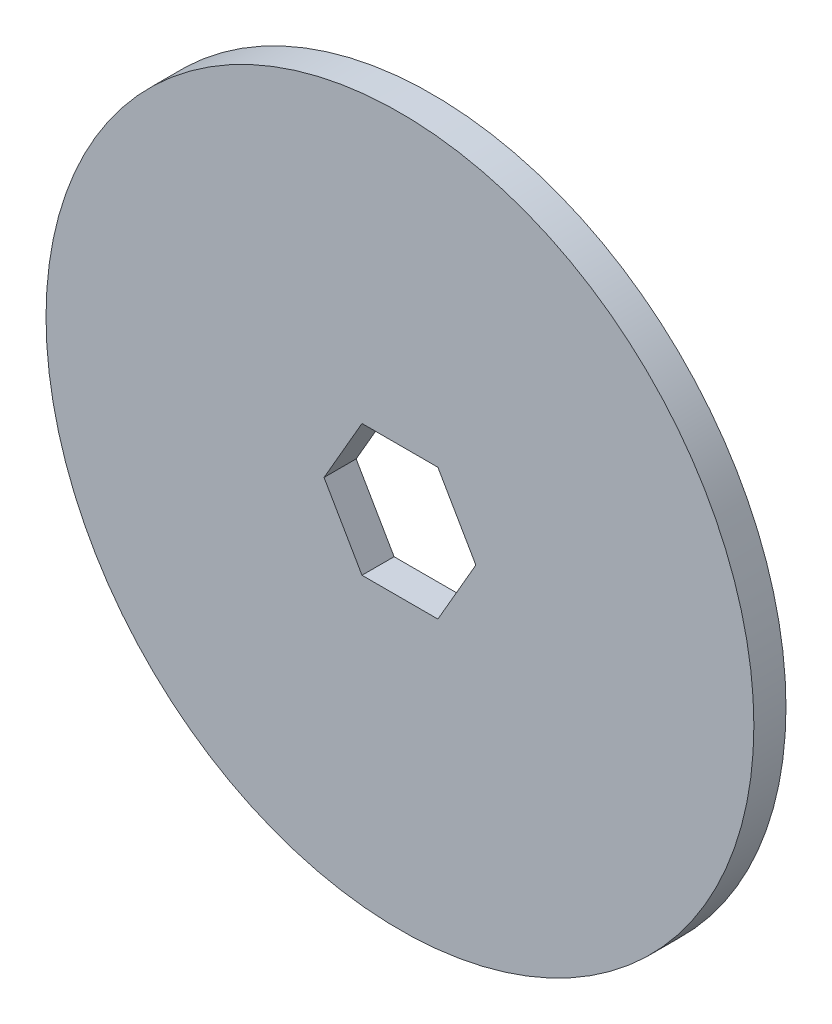
SolidWorks part; units mm, degrees
ref_plane "Front Plane" through (0, 0, 0) normal (0, 0, 1) x (1, 0, 0)
ref_plane "Top Plane" through (0, 0, 0) normal (0, 1, 0) x (1, 0, 0)
ref_plane "Right Plane" through (0, 0, 0) normal (1, 0, 0) x (0, 0, -1)
sketch "Sketch1" plane through (0, 0, 0) normal (0, 0, 1) x (1, 0, 0)
  circle A0 centre (0, 0) radius 35
  dimension "D1" = 70
extrude "Boss-Extrude1" add sketch "Sketch1" along normal blind 3.175
sketch "Sketch2" plane through (0, 0, 3.175) normal (0, 0, 1) x (1, 0, 0)
  line L1 (7.5056, 0) -> (3.7528, 6.5)
  line L2 (3.7528, 6.5) -> (-3.7528, 6.5)
  line L3 (-3.7528, 6.5) -> (-7.5056, 0)
  line L4 (-7.5056, 0) -> (-3.7528, -6.5)
  line L5 (-3.7528, -6.5) -> (3.7528, -6.5)
  line L6 (3.7528, -6.5) -> (7.5056, 0)
  circle A0 centre (0, 0) radius 6.5 construction
  dimension "D1" = 13
extrude "Cut-Extrude1" cut sketch "Sketch2" against normal up to next
